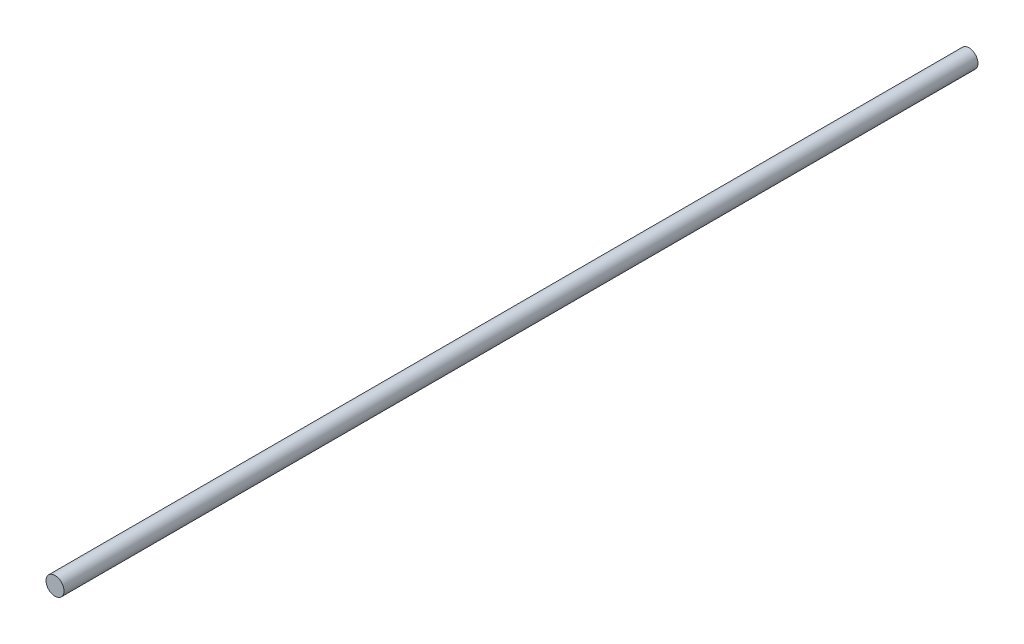
SolidWorks part; units mm, degrees
ref_plane "Front Plane" through (0, 0, 0) normal (0, 0, 1) x (1, 0, 0)
ref_plane "Top Plane" through (0, 0, 0) normal (0, 1, 0) x (1, 0, 0)
ref_plane "Right Plane" through (0, 0, 0) normal (1, 0, 0) x (0, 0, -1)
sketch "Sketch1" plane through (0, 0, 0) normal (0, 0, 1) x (1, 0, 0)
  circle A0 centre (-356.05, 162.7) radius 4.7625 construction
  circle A1 centre (-356.05, 162.7) radius 4.7625
extrude "Extrude1" add sketch "Sketch1" along normal mid plane 482.6
